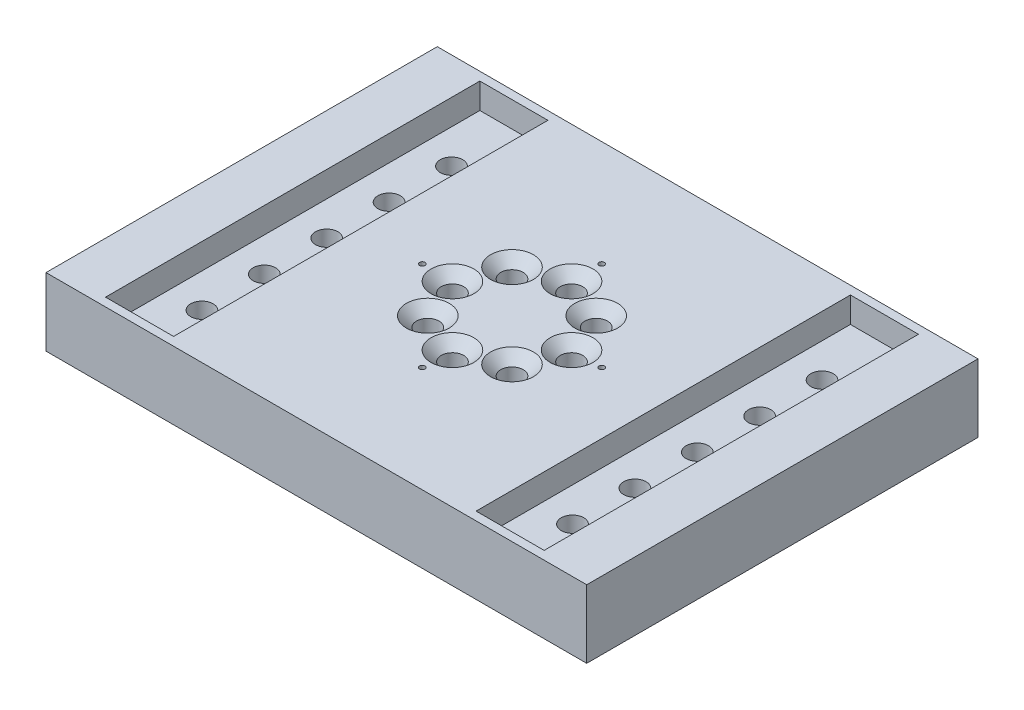
SolidWorks part; units mm, degrees
ref_plane "Front Plane" through (0, 0, 0) normal (0, 0, 1) x (1, 0, 0)
ref_plane "Top Plane" through (0, 0, 0) normal (0, 1, 0) x (1, 0, 0)
ref_plane "Right Plane" through (0, 0, 0) normal (1, 0, 0) x (0, 0, -1)
sketch "Sketch1" plane through (0, 0, 0) normal (0, 1, 0) x (1, 0, 0)
  line L0 (-40.3551, -57.4925) -> (40.3551, -57.4925) construction
  line L1 (79.45, -57.4925) -> (-79.45, -57.4925)
  line L2 (79.45, -57.4925) -> (79.45, 57.4925)
  line L3 (79.45, 57.4925) -> (-79.45, 57.4925)
  line L4 (-79.45, -57.4925) -> (-79.45, 57.4925)
  line L5 (79.45, -57.4925) -> (-79.45, 57.4925) construction
  line L6 (79.45, 57.4925) -> (-79.45, -57.4925) construction
  circle A0 centre (0, 0) radius 17.5 construction
  circle A1 centre (0, 0) radius 26.35 construction
  circle A2 centre (0, 0) radius 44.45 construction
  point P0 (0, 0)
  point P13 (0, -57.4925)
  dimension "D1" = 158.9
  dimension "D2" = 114.9849
extrude "Boss-Extrude1" add sketch "Sketch1" along normal blind 20
sketch "Sketch2" plane through (0, 0, 0) normal (0, -1, 0) x (1, 0, 0)
  circle A0 centre (0, 0) radius 44.45
extrude "Cut-Extrude1" cut sketch "Sketch2" against normal blind 5
sketch "Sketch3" plane through (0, 5, 0) normal (0, -1, 0) x (-1, 0, 0)
  line L0 (-79.45, -57.4925) -> (79.45, 57.4925) construction
  circle A0 centre (0, 0) radius 22.479
extrude "Cut-Extrude2" cut sketch "Sketch3" against normal blind 5.5
sketch "Sketch4" plane through (0, 20, 0) normal (0, 1, 0) x (1, 0, 0)
  line L0 (-17.5, 0) -> (17.5, 0) construction
  line L2 (0, -17.5) -> (0, 17.5) construction
  line L3 (-12.3744, -12.3744) -> (12.3744, 12.3744) construction
  line L4 (-12.3744, 12.3744) -> (12.3744, -12.3744) construction
  circle A0 centre (0, 0) radius 17.5 construction
  point P4 (0, 0)
  point P10 (0, 0)
  point P13 (0, 0)
  point P16 (0, 0)
hole_wizard "CSK for M6 Flat Head Machine Screw1" positions "Sketch7" profile "Sketch8" countersink size "M6" standard "ANSI Metric" end condition through all
sketch "Sketch7" plane through (0, 20, 0) normal (0, 1, 0) x (1, 0, 0)
  point P0 (-17.5, 0)
  point P3 (-12.3744, 12.3744)
  point P6 (0, 17.5)
  point P9 (12.3744, 12.3744)
  point P12 (17.5, 0)
  point P15 (12.3744, -12.3744)
  point P18 (0, -17.5)
  point P21 (-12.3744, -12.3744)
sketch "Sketch8" plane through (-17.5, 20, 0) normal (1, 0, 0) x (0, 0, 1)
  line L0 (0, 0) -> (0, 20)
  line L1 (0, 20) -> (3.3, 20)
  line L2 (3.3, 20) -> (3.3, 3)
  line L3 (3.3, 3) -> (6.3, 0)
  line L5 (6.3, 0) -> (0, 0)
  line L6 (-3.3, 3) -> (-6.3, 0) construction
  line L11 (0, -6.35) -> (0, 107.95) construction
  dimension "Thru Hole Dia." = 6.6
  dimension "Thru Hole Depth" = 20
  dimension "Near C'Sink Dia." = 12.6
  dimension "Near C'Sink Angle" = 90
hole_wizard "Tap Drill for M2x0.4 Tap1" positions "Sketch16" profile "Sketch15" hole size "M2x0.4" standard "ANSI Metric" end condition through all
sketch "Sketch16" plane through (0, 20, 0) normal (0, 1, 0) x (1, 0, 0)
  circle A0 centre (0, 0) radius 26.35 construction
  point P0 (-26.35, 0)
  point P4 (0, 26.35)
  point P6 (0, -26.35)
  point P8 (26.35, 0)
sketch "Sketch15" plane through (-26.35, 20, 0) normal (1, 0, 0) x (0, 0, 1)
  line L0 (0, 0) -> (0, 20)
  line L1 (0, 20) -> (0.8, 20)
  line L2 (0.8, 20) -> (0.8, 0)
  line L5 (0.8, 0) -> (0, 0)
  line L11 (0, -6.35) -> (0, 107.95) construction
  dimension "Thru Hole Dia." = 1.6
  dimension "Thru Hole Depth" = 20
sketch "Sketch18" plane through (0, 20, 0) normal (0, 1, 0) x (1, 0, 0)
  line L0 (44.45, 0) -> (54.45, 0) construction
  line L1 (-44.45, 0) -> (-54.45, 0) construction
  line L3 (-64.45, 55) -> (-44.45, 55)
  line L4 (-64.45, 55) -> (-64.45, -55)
  line L5 (-64.45, -55) -> (-44.45, -55)
  line L6 (-44.45, 55) -> (-44.45, -55)
  line L7 (-64.45, 55) -> (-44.45, -55) construction
  line L8 (-64.45, -55) -> (-44.45, 55) construction
  line L9 (64.45, 55) -> (44.45, 55)
  line L10 (64.45, 55) -> (64.45, -55)
  line L11 (64.45, -55) -> (44.45, -55)
  line L12 (44.45, 55) -> (44.45, -55)
  line L13 (64.45, 55) -> (44.45, -55) construction
  line L14 (64.45, -55) -> (44.45, 55) construction
  circle A0 centre (0, 0) radius 44.45 construction
  dimension "D1" = 110
extrude "Cut-Extrude3" cut sketch "Sketch18" against normal blind 7.5
sketch "Sketch19" plane through (0, 12.5, 0) normal (0, 1, 0) x (1, 0, 0)
  line L0 (-54.45, 55) -> (-54.45, -55) construction
  line L1 (-44.45, 55) -> (-64.45, 55) construction
  line L2 (-64.45, -55) -> (-44.45, -55) construction
  line L3 (54.45, 55) -> (54.45, -55) construction
  line L4 (64.45, 55) -> (44.45, 55) construction
  line L5 (44.45, -55) -> (64.45, -55) construction
  point P12 (-54.45, 36.6667)
  point P13 (-54.45, 18.3333)
  point P14 (-54.45, 0)
  point P15 (-54.45, -18.3333)
  point P16 (-54.45, -36.6667)
  point P17 (54.45, 36.6667)
  point P18 (54.45, 18.3333)
  point P19 (54.45, 0)
  point P20 (54.45, -18.3333)
  point P21 (54.45, -36.6667)
hole_wizard "CSK for M6 Flat Head Machine Screw2" positions "Sketch20" profile "Sketch21" countersink size "M6" standard "ANSI Metric"
sketch "Sketch20" plane through (0, 0, 0) normal (0, -1, 0) x (-1, 0, 0)
  line L0 (-54.45, 55) -> (-54.45, -55) construction
  point P0 (54.45, -36.6667)
  point P3 (54.45, -18.3333)
  point P6 (54.45, 0)
  point P9 (54.45, 18.3333)
  point P12 (54.45, 36.6667)
  point P15 (-54.45, 36.6667)
  point P18 (-54.45, 18.3333)
  point P21 (-54.45, 0)
  point P25 (-54.45, -18.3333)
  point P28 (-54.45, -36.6667)
sketch "Sketch21" plane through (-54.45, 0, 36.6667) normal (1, 0, 0) x (0, 0, -1)
  line L0 (0, 0) -> (0, 21.9828)
  line L1 (0, 21.9828) -> (3.3, 20)
  line L2 (3.3, 20) -> (3.3, 3)
  line L3 (3.3, 3) -> (6.3, 0)
  line L5 (6.3, 0) -> (0, 0)
  line L6 (-3.3, 3) -> (-6.3, 0) construction
  line L10 (0, 21.9828) -> (-3.3, 20) construction
  line L11 (0, -6.35) -> (0, 107.95) construction
  dimension "Hole Dia." = 6.6
  dimension "Hole Depth" = 20
  dimension "Near C'Sink Dia." = 12.6
  dimension "Near C'Sink Angle" = 90
  dimension "Drill Angle" = 118
